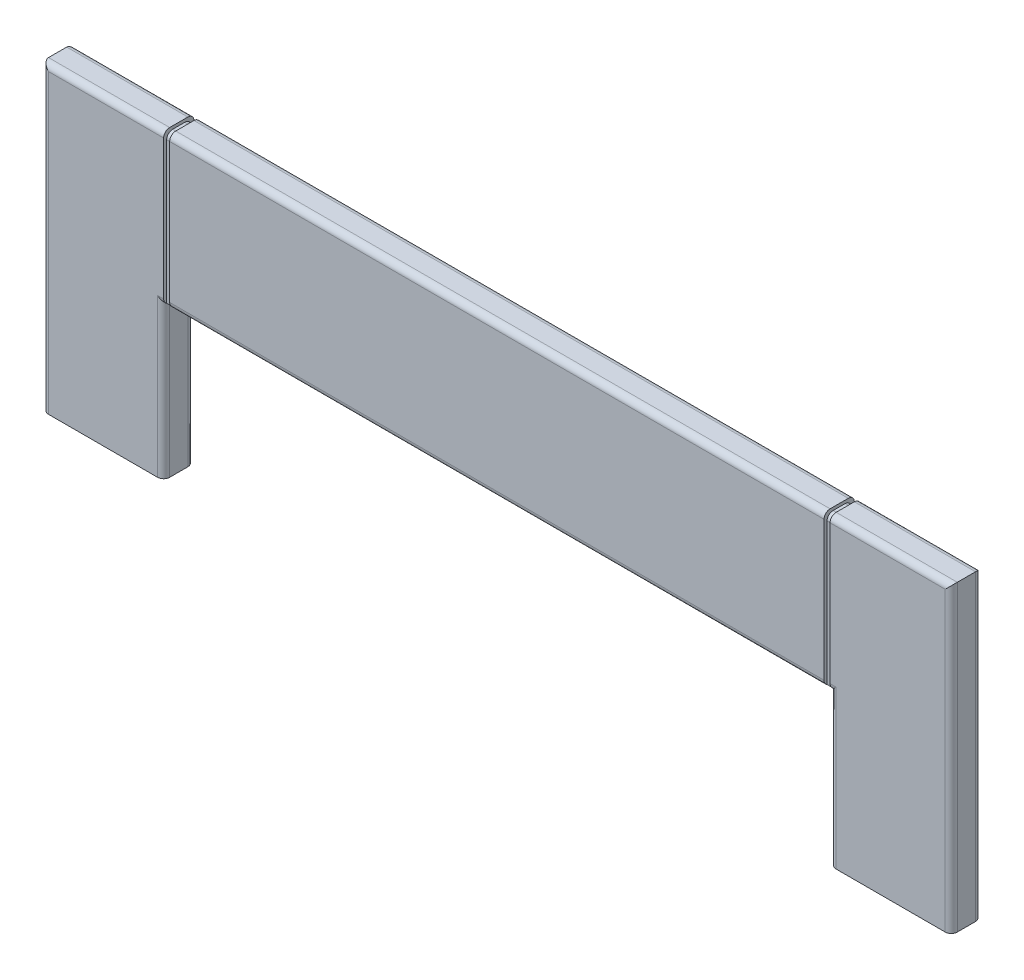
SolidWorks part; units mm, degrees
material "Cedar"
ref_plane "Front Plane" through (0, 0, 0) normal (0, 0, 1) x (1, 0, 0)
ref_plane "Top Plane" through (0, 0, 0) normal (0, 1, 0) x (1, 0, 0)
ref_plane "Right Plane" through (0, 0, 0) normal (1, 0, 0) x (0, 0, -1)
sketch "Sketch1" plane through (0, 0, 0) normal (0, 0, 1) x (1, 0, 0)
  line L0 (-750, 0) -> (750, 0)
  line L1 (750, 0) -> (750, -500)
  line L2 (750, -500) -> (550, -500)
  line L3 (550, -500) -> (550, -250)
  line L4 (550, -250) -> (-550, -250)
  line L5 (-550, -250) -> (-550, -500)
  line L6 (-550, -500) -> (-750, -500)
  line L7 (-750, -500) -> (-750, 0)
  dimension "D1" = 1500
  dimension "D2" = 200
  dimension "D3" = 200
  dimension "D4" = 250
extrude "Boss-Extrude1" add sketch "Sketch1" along normal blind 50
fillet "Fillet1" radius 10 12 edges at (0, 0, 50) (0, 0, 0) (550, -375, 0) (-550, -375, 50) (-550, -375, 0) (550, -375, 50) (0, -250, 50) (0, -250, 0) (750, -250, 0) (-750, -250, 0) (750, -250, 50) (-750, -250, 50)
sketch "Sketch2" plane through (0, 0, 50) normal (0, 0, 1) x (1, 0, 0)
  line L0 (-750, 0) -> (750, 0) construction
  line L1 (-550, -250) -> (-540, -250)
  line L2 (-550, -250) -> (-550, 0)
  line L3 (-550, 0) -> (-540, 0)
  line L4 (-540, -250) -> (-540, 0)
  dimension "D1" = 10
extrude "Cut-Extrude4" cut sketch "Sketch2" against normal blind 5 contours L2 L1 L4 L3
mirror "Mirror1" about plane through (0, 0, 0) normal (1, 0, 0) of "Cut-Extrude4"
sketch "Sketch5" plane through (0, 0, 0) normal (0, 1, 0) x (1, 0, 0)
  line L6 (-550, 0) -> (-540, 0)
  line L7 (-550, 0) -> (-550, -5)
  line L8 (-550, -5) -> (-540, -5)
  line L9 (-540, 0) -> (-540, -5)
  dimension "D1" = 5
  dimension "D2" = 10
extrude "Cut-Extrude16" cut sketch "Sketch5" against normal blind 200
mirror "Mirror5" about plane through (0, 0, 0) normal (1, 0, 0) of "Cut-Extrude16"
sketch "Sketch6" plane through (0, 0, 50) normal (0, 0, 1) x (1, 0, 0)
  line L0 (-750, 0) -> (750, 0) construction
  line L1 (540, 0) -> (550, 0)
  line L2 (540, 0) -> (540, -5)
  line L3 (540, -5) -> (550, -5)
  line L4 (550, 0) -> (550, -5)
  line L5 (550, -248.6603) -> (550, -1.3397) construction
  point P8 (540, -1.3397)
  dimension "D1" = 5
extrude "Cut-Extrude17" cut sketch "Sketch6" against normal blind 50
fillet "Fillet2" radius 10 2 edges at (545, -5, 5) (545, -5, 45)
mirror "Mirror8" about plane through (0, 0, 0) normal (1, 0, 0) of "Cut-Extrude17"
fillet "Fillet3" radius 10 2 edges at (-545, -5, 5) (-545, -5, 45)
